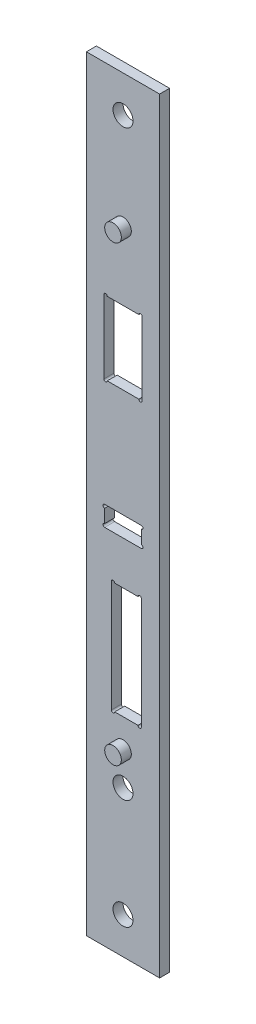
SolidWorks part; units mm, degrees
ref_plane "Face" through (0, 0, 0) normal (0, 0, 1) x (1, 0, 0)
ref_plane "Dessus" through (0, 0, 0) normal (0, 1, 0) x (1, 0, 0)
ref_plane "Droite" through (0, 0, 0) normal (1, 0, 0) x (0, 0, -1)
sketch "Esquisse1" plane through (0, 0, 0) normal (0, 0, 1) x (1, 0, 0)
  line L0 (0, 0) -> (-61.9891, 0) construction
  line L1 (-11, 115) -> (11, 115)
  line L2 (-11, 115) -> (-11, -115)
  line L3 (-11, -115) -> (11, -115)
  line L4 (11, 115) -> (11, -115)
  line L5 (-61.9891, 0) -> (0, 0) construction
  line L6 (0, 0) -> (0, -71.1874) construction
  dimension "D1" = 22
  dimension "D2" = 230
extrude "Extrusion1" add sketch "Esquisse1" along normal mid plane 3
hole_wizard "Diamètre du perçage Ø6.0 (6)1" positions "Esquisse3" profile "Esquisse5" hole size "Ø6.0" standard "ISO"
sketch "Esquisse3" plane through (0, 0, 1.5) normal (0, 0, 1) x (1, 0, 0)
  line L0 (11, 115) -> (-11, 115) construction
  line L1 (11, -115) -> (11, 115) construction
  line L2 (-11, -115) -> (11, -115) construction
  point P0 (0, 104)
  point P7 (0, -71)
  point P10 (0, -104)
  point P13 (0, -115)
  dimension "D1" = 11
  dimension "D2" = 11
  dimension "D3" = 11
  dimension "D4" = 33
sketch "Esquisse5" plane through (0, 104, 1.5) normal (1, 0, 0) x (0, -1, 0)
  line L0 (0, 0) -> (0, 4.8026)
  line L1 (0, 4.8026) -> (3, 3)
  line L2 (3, 3) -> (3, 0)
  line L5 (3, 0) -> (0, 0)
  line L10 (0, 4.8026) -> (-3, 3) construction
  line L11 (0, -6.35) -> (0, 107.95) construction
  dimension "Diamètre du perçage" = 6
  dimension "Profondeur du perçage" = 3
  dimension "Angle de pointe" = 118
sketch "Esquisse7" plane through (0, 0, 1.5) normal (0, 0, 1) x (1, 0, 0)
  line L0 (0, 0) -> (0, 30.0857) construction
  line L1 (-4.75, 54.5) -> (4.75, 54.5)
  line L2 (-5.75, 54.5) -> (-5.75, 32.5)
  line L3 (-4.75, 32.5) -> (4.75, 32.5)
  line L4 (5.75, 54.5) -> (5.75, 32.5)
  arc A0 (-4.75, 54.5) -> (-5.75, 54.5) centre (-5.25, 54.5) ccw
  arc A1 (5.75, 54.5) -> (4.75, 54.5) centre (5.25, 54.5) ccw
  arc A2 (-5.75, 32.5) -> (-4.75, 32.5) centre (-5.25, 32.5) ccw
  arc A3 (5.75, 32.5) -> (4.75, 32.5) centre (5.25, 32.5) cw
  dimension "D4" = 1
  dimension "D5" = 1
  dimension "D7" = 1
  dimension "D1" = 11.5
  dimension "D2" = 22
  dimension "D3" = 32.5
extrude "Enlèv. mat.-Extru.1" cut sketch "Esquisse7" against normal up to next
sketch "Esquisse8" plane through (0, 0, 1.5) normal (0, 0, 1) x (1, 0, 0)
  line L0 (0, 0) -> (0, 20.99) construction
  line L1 (-5.5, 0) -> (5.5, 0)
  line L2 (-5.5, -1) -> (-5.5, -5)
  line L3 (-5.5, -6) -> (5.5, -6)
  line L4 (5.5, -1) -> (5.5, -5)
  line L5 (11, 115) -> (-11, 115) construction
  line L6 (11, -115) -> (11, 115) construction
  line L7 (0, 0) -> (0, -29.4953) construction
  arc A0 (-5.5, 0) -> (-5.5, -1) centre (-5.5, -0.5) ccw
  arc A1 (-5.5, -5) -> (-5.5, -6) centre (-5.5, -5.5) ccw
  arc A2 (5.5, 0) -> (5.5, -1) centre (5.5, -0.5) cw
  arc A3 (5.5, -5) -> (5.5, -6) centre (5.5, -5.5) cw
  dimension "D3" = 1
  dimension "D4" = 1
  dimension "D1" = 11
  dimension "D2" = 6
  dimension "D5" = 115
  dimension "D6" = 5.5
  dimension "D7" = 11
extrude "Enlèv. mat.-Extru.2" cut sketch "Esquisse8" against normal up to next
sketch "Esquisse9" plane through (0, 0, 1.5) normal (0, 0, 1) x (1, 0, 0)
  line L0 (1, 0) -> (1, -46.0339) construction
  line L1 (-2.5, -19) -> (4.5, -19)
  line L2 (-3.5, -19) -> (-3.5, -52.5)
  line L3 (-2.5, -52.5) -> (4.5, -52.5)
  line L4 (5.5, -19) -> (5.5, -52.5)
  line L5 (11, 115) -> (-11, 115) construction
  line L6 (11, -115) -> (11, 115) construction
  line L8 (-11, -115) -> (11, -115) construction
  arc A0 (-2.5, -19) -> (-3.5, -19) centre (-3, -19) ccw
  arc A1 (5.5, -52.5) -> (4.5, -52.5) centre (5, -52.5) cw
  arc A2 (-3.5, -52.5) -> (-2.5, -52.5) centre (-3, -52.5) ccw
  arc A3 (4.5, -19) -> (5.5, -19) centre (5, -19) cw
  dimension "D4" = 1
  dimension "D5" = 10
  dimension "D6" = 1
  dimension "D7" = 0.5
  dimension "D1" = 9
  dimension "D2" = 33.5
  dimension "D3" = 134
extrude "Enlèv. mat.-Extru.3" cut sketch "Esquisse9" against normal up to next
sketch "Esquisse10" plane through (0, 0, 1.5) normal (0, 0, 1) x (1, 0, 0)
  line L0 (11, -115) -> (11, 115) construction
  line L1 (11, 115) -> (-11, 115) construction
  line L3 (0, 0) -> (0, -123.6653) construction
  line L5 (5.5, 0) -> (-5.5, 0) construction
  line L6 (0, 0) -> (0, 7.7599) construction
  circle A0 centre (0, 75) radius 2.5
  circle A1 centre (0, -61) radius 2.5
  dimension "D1" = 5
  dimension "D4" = 5
  dimension "D2" = 11
  dimension "D3" = 40
  dimension "D5" = 136
extrude "Extrusion2" add sketch "Esquisse10" along normal blind 3
